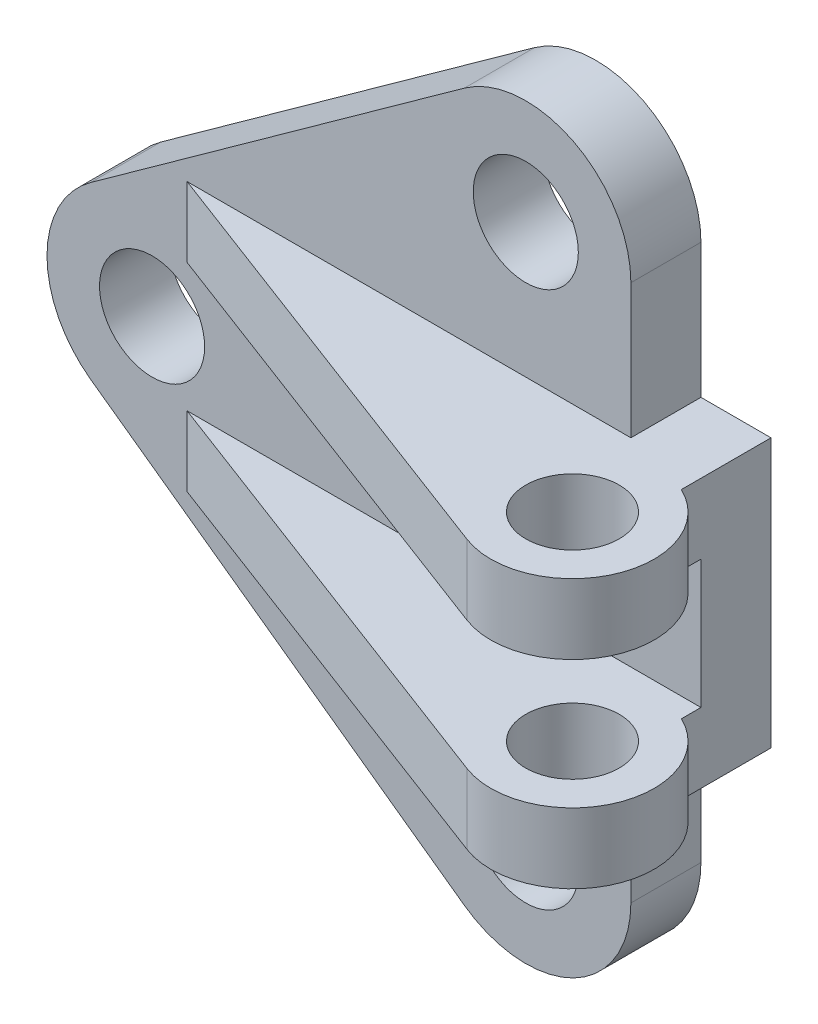
SolidWorks part; units mm, degrees
ref_plane "Front Plane" through (0, 0, 0) normal (0, 0, 1) x (1, 0, 0)
ref_plane "Top Plane" through (0, 0, 0) normal (0, 1, 0) x (1, 0, 0)
ref_plane "Right Plane" through (0, 0, 0) normal (1, 0, 0) x (0, 0, -1)
sketch "Sketch1" plane through (0, 0, 0) normal (0, 0, 1) x (1, 0, 0)
  line L3 (-10.5054, 14.6163) -> (53.4946, 60.6163)
  line L4 (-10.5054, -14.6163) -> (53.4946, -60.6163)
  line L5 (82, 46) -> (82, -46)
  circle A0 centre (0, 0) radius 9
  arc A1 (-10.5054, 14.6163) -> (-10.5054, -14.6163) centre (0, 0) ccw
  circle A2 centre (64, 46) radius 9
  arc A3 (82, 46) -> (53.4946, 60.6163) centre (64, 46) ccw
  circle A4 centre (64, -46) radius 9
  arc A5 (53.4946, -60.6163) -> (82, -46) centre (64, -46) ccw
  dimension "D1" = 18
  dimension "D2" = 36
  dimension "D4" = 18
  dimension "D5" = 36
  dimension "D6" = 36
  dimension "D7" = 18
extrude "Boss-Extrude1" add sketch "Sketch1" along normal blind 12
sketch "Sketch6" plane through (82, 0, 0) normal (1, 0, 0) x (0, 0, -1)
  line L1 (-12, -46) -> (-12, 46) construction
  line L3 (0, 23) -> (-12, 23)
  line L4 (0, 23) -> (0, -23)
  line L5 (0, -23) -> (-12, -23)
  line L6 (-12, 23) -> (-12, -23)
  line L7 (0, 23) -> (-12, -23) construction
  line L8 (0, -23) -> (-12, 23) construction
  point P5 (-6, 0)
  dimension "D1" = 46
extrude "Boss-Extrude5" add sketch "Sketch6" along normal blind 12 contours L4 L3 L6 L5
sketch "Sketch7" plane through (0, -23, 0) normal (0, -1, 0) x (1, 0, 0)
  line L2 (6, 12) -> (94, 12)
  line L3 (94, 12) -> (94, 15.3509)
  line L4 (-10.5054, 12) -> (53.4946, 12) construction
  line L5 (83.0542, 41.0973) -> (6, 12)
  circle A0 centre (88, 28) radius 8
  arc A1 (94, 15.3509) -> (83.0542, 41.0973) centre (88, 28) ccw
  dimension "D1" = 16
extrude "Boss-Extrude17" add sketch "Sketch7" against normal blind 12
mirror "Mirror2" about plane through (0, 0, 0) normal (0, 1, 0) of "Boss-Extrude17"
